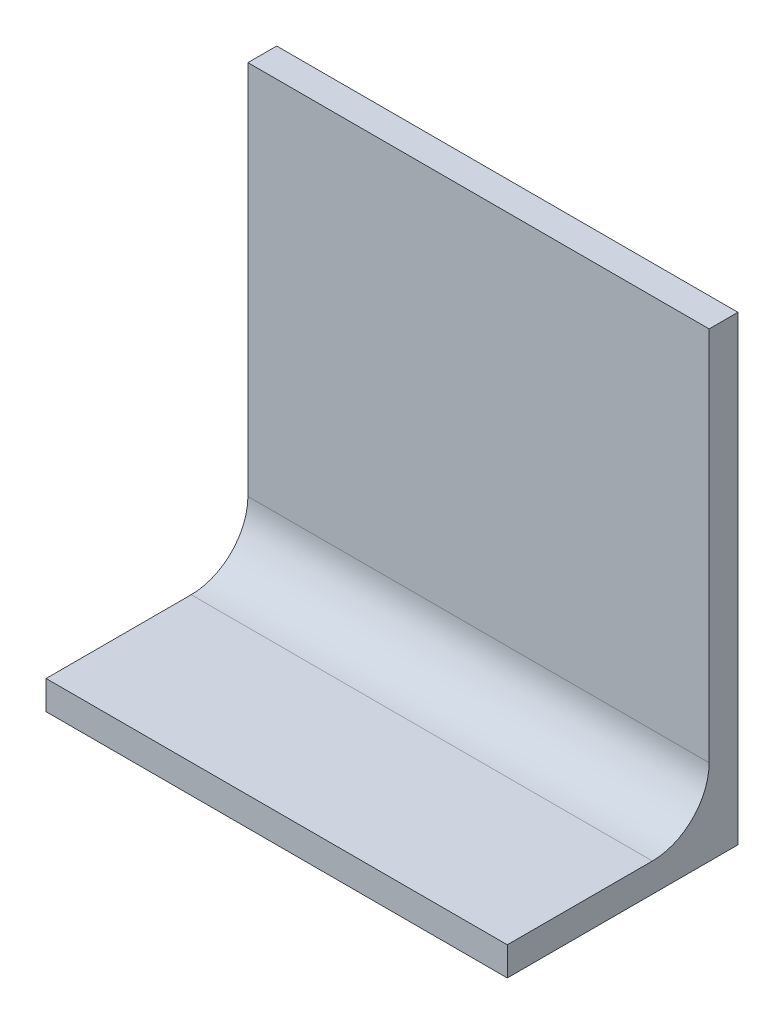
SolidWorks part; units mm, degrees
ref_plane "Front" through (0, 0, 0) normal (0, 0, 1) x (1, 0, 0)
ref_plane "Top" through (0, 0, 0) normal (0, 1, 0) x (1, 0, 0)
ref_plane "Right" through (0, 0, 0) normal (1, 0, 0) x (0, 0, -1)
sketch "Sketch1" plane through (0, 0, 0) normal (1, 0, 0) x (0, 0, -1)
  line L0 (0, 0) -> (22.23, 0)
  line L1 (22.23, 0) -> (22.23, 47.63)
  line L2 (0, -3.17) -> (25.4, -3.17)
  line L3 (25.4, -3.17) -> (25.4, 47.63)
  line L4 (0, 0) -> (0, -3.17)
  line L5 (22.23, 47.63) -> (25.4, 47.63)
  dimension "D2" = 25.4
  dimension "D3" = 50.8
  dimension "D1" = 3.17
extrude "Boss-Extrude1" add sketch "Sketch1" along normal mid plane 50.8
fillet "Fillet1" radius 6.25 1 edges at (0, 0, -22.23)
